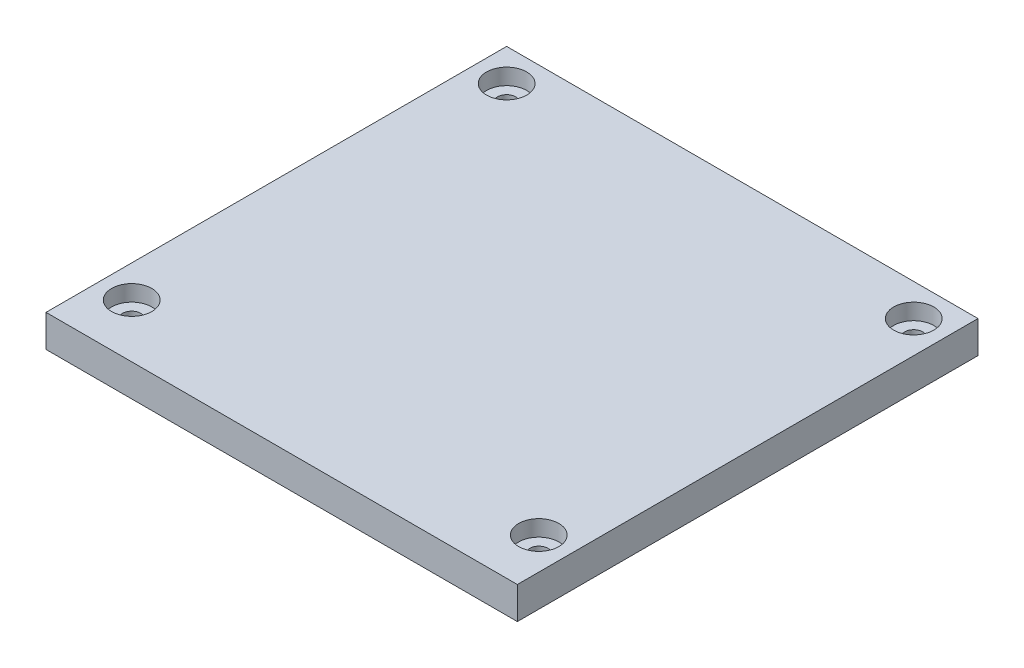
SolidWorks part; units mm, degrees
ref_plane "Спереди" through (0, 0, 0) normal (0, 0, 1) x (1, 0, 0)
ref_plane "Сверху" through (0, 0, 0) normal (0, 1, 0) x (1, 0, 0)
ref_plane "Справа" through (0, 0, 0) normal (1, 0, 0) x (0, 0, -1)
sketch "Sketch1" plane through (0, 0, 0) normal (0, 1, 0) x (1, 0, 0)
  line L1 (44, -41) -> (-44, -41)
  line L2 (44, -41) -> (44, 41)
  line L3 (44, 41) -> (-44, 41)
  line L4 (-44, -41) -> (-44, 41)
  line L5 (44, -41) -> (-44, 41) construction
  line L6 (44, 41) -> (-44, -41) construction
  point P0 (0, 0)
  dimension "D1" = 88
  dimension "D2" = 82
extrude "Boss-Extrude1" add sketch "Sketch1" along normal blind 3
sketch "Sketch2" plane through (0, 3, 0) normal (0, 1, 0) x (1, 0, 0)
  line L0 (-44, 41) -> (-44, -41) construction
  line L1 (38, -35) -> (-38, -35) construction
  line L2 (38, -35) -> (38, 35) construction
  line L3 (38, 35) -> (-38, 35) construction
  line L4 (-38, -35) -> (-38, 35) construction
  line L5 (38, -35) -> (-38, 35) construction
  line L6 (38, 35) -> (-38, -35) construction
  line L7 (44, 41) -> (-44, 41) construction
  circle A0 centre (-38, 35) radius 1.7
  circle A1 centre (38, 35) radius 1.7
  circle A2 centre (38, -35) radius 1.7
  circle A3 centre (-38, -35) radius 1.7
  point P0 (0, 0)
  dimension "D3" = 3.4
  dimension "D1" = 6
  dimension "D2" = 6
extrude "Cut-Extrude1" cut sketch "Sketch2" against normal through all
sketch "Sketch4" plane through (0, 0, 0) normal (0, -1, 0) x (1, 0, 0)
  line L0 (-44, -41) -> (-44, 41) construction
  line L1 (40.6, 37.6) -> (-40.6, 37.6)
  line L2 (40.6, 37.6) -> (40.6, -37.6)
  line L3 (40.6, -37.6) -> (-40.6, -37.6)
  line L4 (-40.6, 37.6) -> (-40.6, -37.6)
  line L5 (40.6, 37.6) -> (-40.6, -37.6) construction
  line L6 (40.6, -37.6) -> (-40.6, 37.6) construction
  line L7 (44, -41) -> (-44, -41) construction
  line L9 (37.6, 34.6) -> (-37.6, 34.6)
  line L10 (37.6, 34.6) -> (37.6, -34.6)
  line L11 (37.6, -34.6) -> (-37.6, -34.6)
  line L12 (-37.6, 34.6) -> (-37.6, -34.6)
  line L13 (37.6, 34.6) -> (-37.6, -34.6) construction
  line L14 (37.6, -34.6) -> (-37.6, 34.6) construction
  point P0 (0, 0)
  point P10 (0, 0)
  dimension "D1" = 3.4
  dimension "D2" = 3.4
  dimension "D3" = 3
  dimension "D4" = 3
extrude "Boss-Extrude2" add sketch "Sketch4" along normal blind 2
sketch "Sketch6" plane through (0, 3, 0) normal (0, 1, 0) x (1, 0, 0)
  line L0 (44, -41) -> (44, 41) construction
  circle A0 centre (-38, 35) radius 6
  circle A1 centre (-38, -35) radius 6
  circle A2 centre (38, -35) radius 6
  circle A3 centre (38, 35) radius 6
extrude "Cut-Extrude5" cut sketch "Sketch6" against normal through all from offset 3 offset against normal yes
sketch "Sketch7" plane through (0, 0, 41) normal (0, 0, 1) x (1, 0, 0)
  line L0 (-44, 3) -> (-44, 0)
  line L1 (-44, 0) -> (44, 0)
  line L2 (44, 0) -> (44, 3)
  line L3 (44, 3) -> (-44, 3)
extrude "Boss-Extrude3" add sketch "Sketch7" along normal blind 4
sketch "Sketch8" plane through (0, 3, 0) normal (0, 1, 0) x (1, 0, 0)
  line L0 (-44, -41) -> (-44, -45)
  line L1 (-44, -45) -> (44, -45)
  line L2 (44, -41) -> (44, 41)
  line L3 (44, 41) -> (-44, 41)
  line L4 (-44, -41) -> (-44, 41)
  line L5 (44, -41) -> (-44, 41) construction
  line L6 (44, 41) -> (-44, -41) construction
  line L7 (44, -45) -> (44, -41)
  circle A1 centre (-38, 35) radius 3.75
  circle A3 centre (38, 35) radius 3.75
  circle A6 centre (-38, -35) radius 3.75
  circle A7 centre (38, -35) radius 3.75
  point P0 (0, 0)
  dimension "D1" = 7.5
extrude "Boss-Extrude4" add sketch "Sketch8" along normal blind 3
